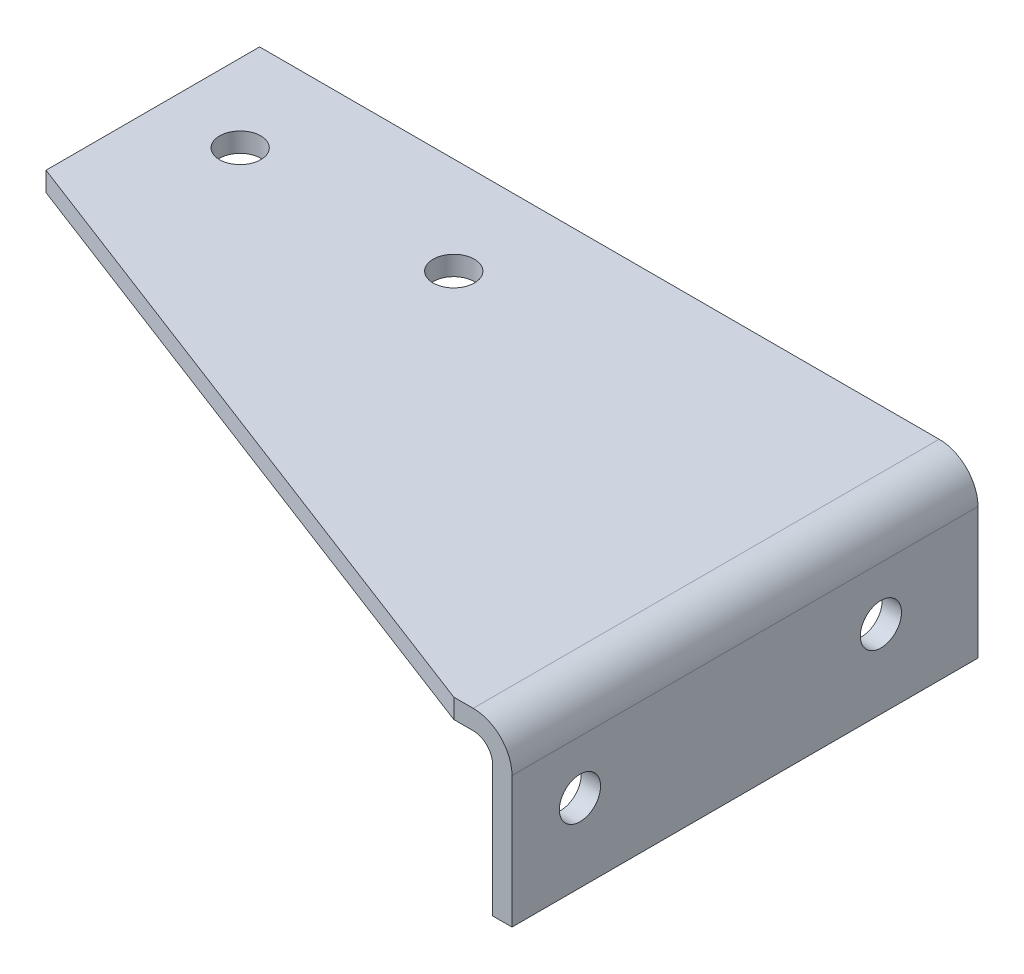
SolidWorks part; units mm, degrees
ref_plane "Front" through (0, 0, 0) normal (0, 0, 1) x (1, 0, 0)
ref_plane "Top" through (0, 0, 0) normal (0, 1, 0) x (1, 0, 0)
ref_plane "Side" through (0, 0, 0) normal (1, 0, 0) x (0, 0, -1)
sketch "Sketch1" plane through (0, 0, 0) normal (0, 0, 1) x (1, 0, 0)
  line L0 (-228.6, 0) -> (-6.35, 0)
  line L1 (0, -6.35) -> (0, -49.276)
  arc A0 (-6.35, 0) -> (0, -6.35) centre (-6.35, -6.35) cw
  point P6 (0, 0)
  dimension "D3" = 6.35
  dimension "D1" = 228.6
  dimension "D2" = 49.276
extrude "Base-Extrude-Thin" add sketch "Sketch1" along normal blind 152.4 thin thin type one direction reverse wall 6.35
sketch "Sketch2" plane through (0, 0, 0) normal (0, 1, 0) x (1, 0, 0)
  line L0 (-228.6, -69.85) -> (-12.7, -152.4)
  line L1 (-228.6, -152.4) -> (-228.6, 0) construction
  line L2 (6.35, -152.4) -> (6.35, 0) construction
  line L4 (-228.6, -152.4) -> (-6.35, -152.4) construction
  line L5 (-730.25, -69.85) -> (-107.95, -69.85) construction
  dimension "D1" = 19.05
extrude "Cut cnr" cut sketch "Sketch2" against normal through all and the other way through all flip side to cut
hole_wizard "Hole-flg" positions "Sketch5" profile "Sketch4" legacy end condition through all
sketch "Sketch5" plane through (6.35, 0, 0) normal (1, 0, 0) x (0, 0, -1)
  line L0 (-130.175, -23.8125) -> (-31.75, -23.8125) construction
  line L1 (-152.4, 0) -> (0, 0) construction
  line L2 (0, -6.35) -> (0, -49.276) construction
  point P0 (-130.175, -23.8125)
  point P1 (-31.75, -23.8125)
  dimension "D1" = 23.8125
  dimension "D2" = 31.75
  dimension "D3" = 98.425
sketch "Sketch4" plane through (6.35, -23.8125, 130.175) normal (0, 1, 0) x (0, 0, -1)
  line L0 (0, 0) -> (0, 234.95)
  line L1 (0, 234.95) -> (6.731, 234.95)
  line L2 (6.731, 234.95) -> (6.731, 0)
  line L3 (6.731, 0) -> (0, 0)
  line L4 (0, 110) -> (0, -10) construction
  dimension "Diameter" = 13.462
  dimension "Depth" = 234.95
hole_wizard "Hole-top" positions "Sketch9" profile "Sketch8" legacy
sketch "Sketch9" plane through (0, 6.35, 0) normal (0, 1, 0) x (-1, 0, 0)
  point P0 (203.2, 31.75)
  point P8 (133.35, 31.75)
sketch "Sketch8" plane through (-203.2, 6.35, 31.75) normal (1, 0, 0) x (0, 0, 1)
  line L0 (0, 0) -> (0, 25.4)
  line L1 (0, 25.4) -> (6.7469, 25.4)
  line L2 (6.7469, 25.4) -> (6.7469, 0)
  line L3 (6.7469, 0) -> (0, 0)
  line L4 (0, 110) -> (0, -10) construction
  dimension "Diameter" = 13.4937
  dimension "Depth" = 25.4
mirror "Mirror All1" [suppressed]
sketch "Sketch10" plane through (0, 0, 0) normal (0, 1, 0) x (1, 0, 0)
  line L0 (6.35, -76.2) -> (-228.6, -34.925)
  line L1 (6.35, -152.4) -> (6.35, 0) construction
  line L2 (-228.6, -69.85) -> (-228.6, 0) construction
extrude "Cut-lh" [suppressed] cut sketch "Sketch10" against normal through all and the other way through all
